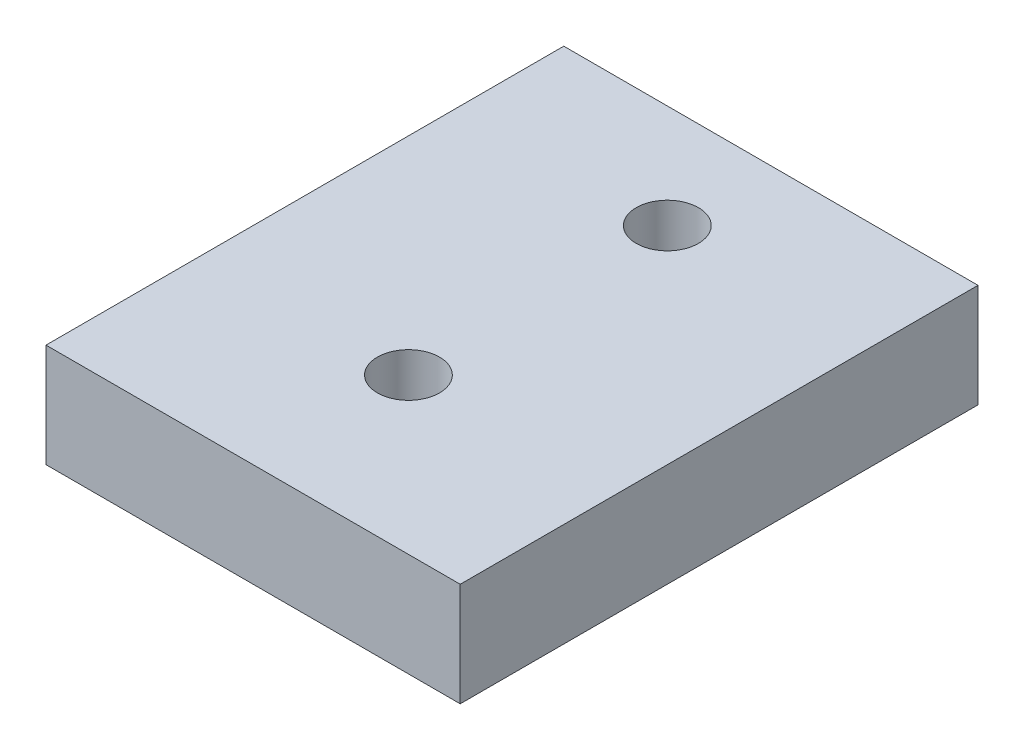
SolidWorks part; units mm, degrees
ref_plane "Front Plane" through (0, 0, 0) normal (0, 0, 1) x (1, 0, 0)
ref_plane "Top Plane" through (0, 0, 0) normal (0, 1, 0) x (1, 0, 0)
ref_plane "Right Plane" through (0, 0, 0) normal (1, 0, 0) x (0, 0, -1)
sketch "Sketch1" plane through (0, 0, 0) normal (0, 1, 0) x (1, 0, 0)
  line L36 (0, 0) -> (40, 0)
  line L41 (40, 0) -> (40, 50)
  line L42 (40, 50) -> (0, 50)
  line L43 (0, 50) -> (0, 0)
  circle A1 centre (20, 15) radius 3
  circle A6 centre (20, 40) radius 3
  point P3 (0, 0)
  point P5 (0, 0)
  point P6 (0, 0)
  point P7 (0, 0)
  dimension "D1" = 10
  dimension "D2" = 15
extrude "Boss-Extrude1" add sketch "Sketch1" along normal blind 10
